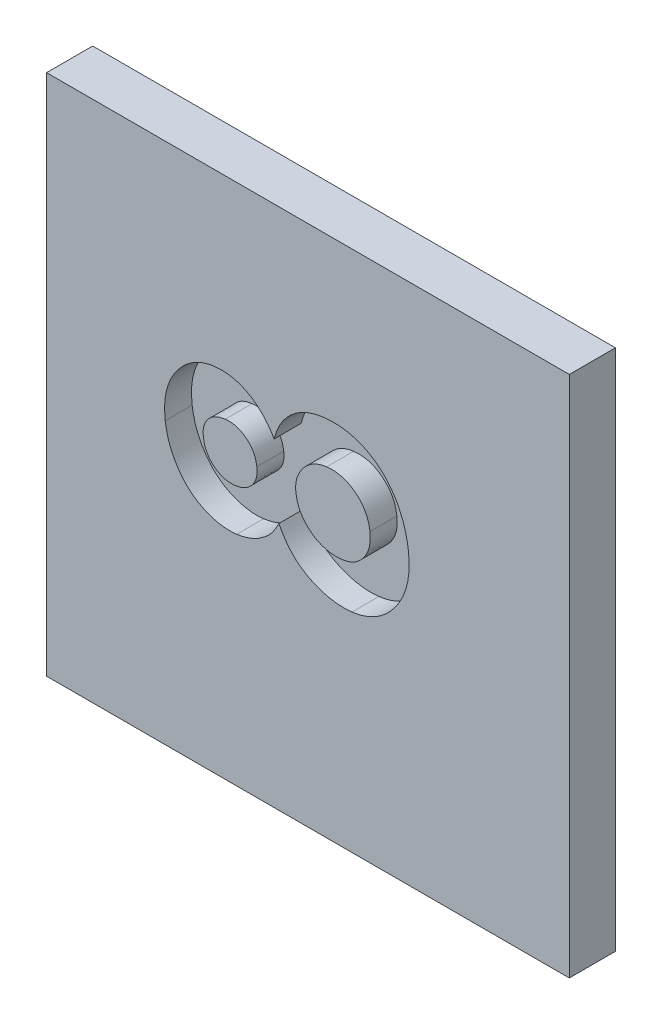
SolidWorks part; units mm, degrees
material "1060 Legierung"
ref_plane "Ebene vorne" through (0, 0, 0) normal (0, 0, 1) x (1, 0, 0)
ref_plane "Ebene oben" through (0, 0, 0) normal (0, 1, 0) x (1, 0, 0)
ref_plane "Ebene rechts" through (0, 0, 0) normal (1, 0, 0) x (0, 0, -1)
sketch "Skizze1" plane through (0, 0, 0) normal (0, 0, 1) x (1, 0, 0)
  line L1 (-50, -106) -> (86, -106)
  line L2 (-50, -106) -> (-50, 30)
  line L3 (-50, 30) -> (86, 30)
  line L4 (86, -106) -> (86, 30)
  line L5 (-50, -106) -> (86, 30) construction
  line L6 (-50, 30) -> (86, -106) construction
  point P0 (18, -38)
  dimension "D1" = 136
  dimension "D2" = 136
extrude "Aufsatz-Linear austragen1" add sketch "Skizze1" along normal blind 12
sketch "Skizze2" plane through (31.8172, 33.5361, 12) normal (0, 0, 1) x (-0.1219, 0.9925, 0)
  text T0 "8" font "Century Gothic" height 60
  point P1 (-81.7444, 9.8318)
  point P2 (-83.8462, 1.5128)
  point P3 (-85.1851, -2.8637)
extrude "Schnitt-Linear austragen2" cut sketch "Skizze2" against normal blind 7
sketch3d "3D-Skizze1"
  point P0 (-50, 30, 8.5)
